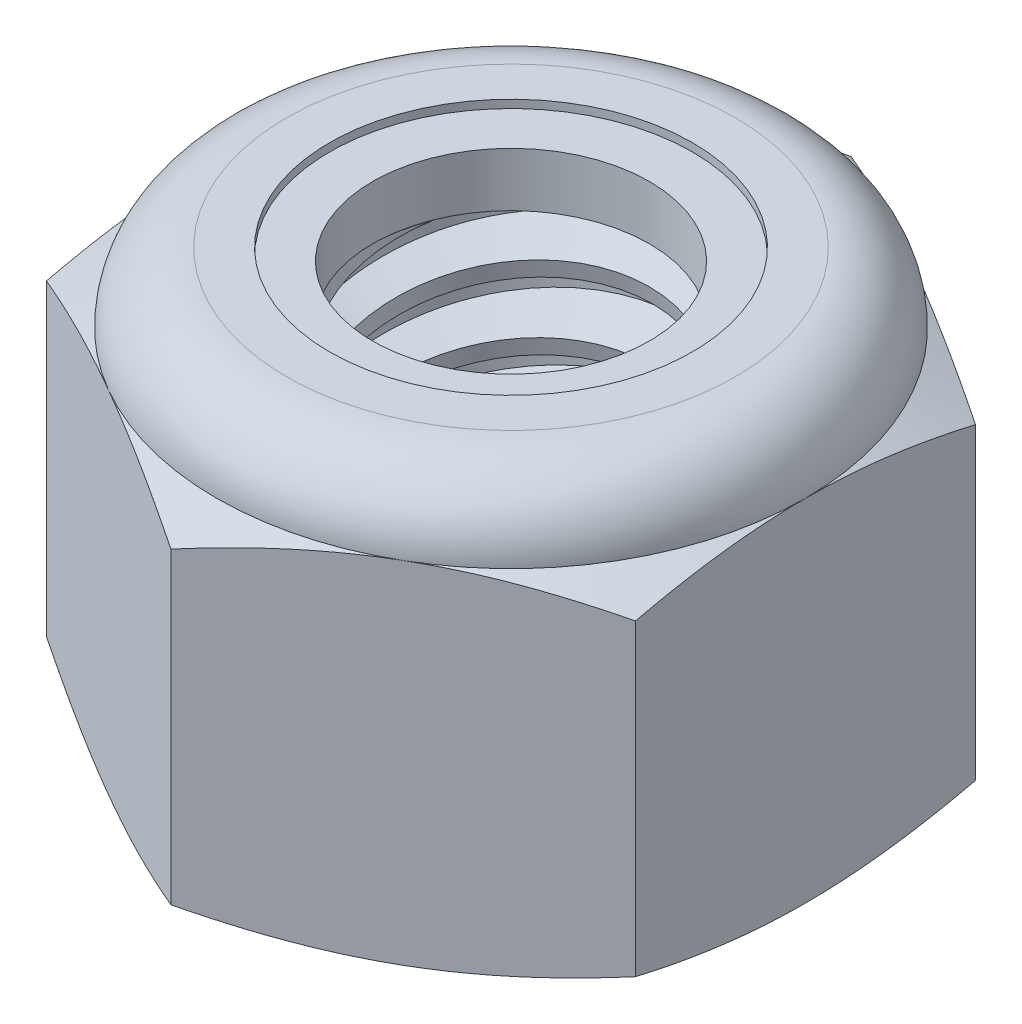
SolidWorks part; units mm, degrees
ref_plane "Front" through (0, 0, 0) normal (0, 0, 1) x (1, 0, 0)
ref_plane "Top" through (0, 0, 0) normal (0, 1, 0) x (1, 0, 0)
ref_plane "Right" through (0, 0, 0) normal (1, 0, 0) x (0, 0, -1)
sketch "Sketch1" plane through (0, 0, 0) normal (0, 1, 0) x (1, 0, 0)
  line L1 (0, 6.4158) -> (-5.5563, 3.2079)
  line L2 (-5.5563, 3.2079) -> (-5.5563, -3.2079)
  line L3 (-5.5563, -3.2079) -> (0, -6.4158)
  line L4 (0, -6.4158) -> (5.5562, -3.2079)
  line L5 (5.5562, -3.2079) -> (5.5562, 3.2079)
  line L6 (5.5562, 3.2079) -> (0, 6.4158)
  circle A0 centre (0, 0) radius 5.5563 construction
  dimension "Hex Flats" = 11.1125
extrude "Extrude1" add sketch "Sketch1" along normal blind 7.9375
sketch "Sketch2" plane through (0, 0, 0) normal (1, 0, 0) x (0, 0, -1)
  line L0 (-3.175, 0) -> (-3.175, 7.9375) construction
  line L1 (0, 0) -> (3.175, 0)
  line L2 (0, 0) -> (0, 7.9375)
  line L3 (0, 7.9375) -> (3.175, 7.9375)
  line L4 (3.175, 0) -> (3.175, 7.9375)
  line L5 (-3.2079, 7.9375) -> (3.2079, 7.9375) construction
  line L7 (0, -3.175) -> (0, 0) construction
  dimension "Thread Dia" = 6.35
revolve "Revolve1" add sketch "Sketch2" angle 360 about L7
sketch "Sketch3" plane through (0, 0, 0) normal (1, 0, 0) x (0, 0, -1)
  line L0 (3.175, 7.9375) -> (-3.175, 7.9375) construction
  line L1 (-3.175, 7.9375) -> (-3.175, 6.6675) construction
  line L2 (-3.175, 6.6675) -> (3.175, 7.9375) construction
  line L3 (3.175, 7.9375) -> (3.2061, 7.7818) construction
  line L4 (3.2061, 7.7818) -> (3.4241, 6.6922)
  line L5 (3.4241, 6.6922) -> (2.6722, 6.9465)
  line L6 (2.6722, 6.9465) -> (2.6099, 7.2579)
  line L7 (2.6099, 7.2579) -> (3.2061, 7.7818)
  line L8 (2.641, 7.1022) -> (3.3151, 7.237) construction
  line L9 (3.175, 7.9375) -> (3.175, 7.209) construction
  line L10 (3.175, 7.209) -> (-3.175, 5.939) construction
  line L11 (-3.175, 5.939) -> (-3.175, 6.6675) construction
  line L12 (-0.2727, 7.9375) -> (0.2727, 5.2105) construction
  line L13 (-3.175, 0) -> (-3.175, 7.9375) construction
  line L14 (0, 7.9375) -> (3.175, 7.9375) construction
  line L15 (3.175, 0) -> (3.175, 7.9375) construction
  point P13 (0, 6.574)
  dimension "D1" = 0.1588
  dimension "D2" = 0.3175
  dimension "Thread Pitch" = 1.27
  dimension "D4" = 60
  dimension "D5" = 1.27
revolve "Cut-Revolve1" cut sketch "Sketch3" angle 360 about L12
pattern_linear "LPattern1" count 6 spacing 1.27 along (0, -1, 0) count 2 spacing 1.27 along (0, 1, 0) of "Cut-Revolve1"
sketch "Sketch4" plane through (0, 0, 0) normal (1, 0, 0) x (0, 0, -1)
  line L0 (0, 7.9375) -> (3.175, 7.9375)
  line L1 (3.175, 7.9375) -> (2.6099, 7.674)
  line L2 (2.6099, 7.674) -> (2.6099, 0.2635)
  line L3 (2.6099, 0.2635) -> (3.175, 0)
  line L4 (3.175, 0) -> (0, 0)
  line L5 (0, 0) -> (0, 7.9375)
  line L6 (3.175, 0) -> (3.175, 7.9375) construction
  line L7 (0, 7.9375) -> (3.175, 7.9375) construction
  line L8 (0, 0) -> (3.175, 0) construction
  line L9 (0, 0) -> (0, 7.9375) construction
  line L10 (0, 7.9375) -> (0, 8.561) construction
  dimension "D1" = 25
revolve "Cut-Revolve2" cut sketch "Sketch4" angle 360 about L10
combine bodies "Combine1" operation type subtract main body 112 bodies to subtract 111
sketch "Sketch5" plane through (0, 0, 0) normal (1, 0, 0) x (0, 0, -1)
  line L0 (0, 0) -> (5.5563, 0)
  line L1 (5.5563, 0) -> (6.4158, 0.4008)
  line L2 (6.4158, 0.4008) -> (6.4158, 6.2138)
  line L3 (6.4158, 6.2138) -> (5.5563, 6.6146)
  line L4 (4.2333, 7.9375) -> (4.2333, 9.2075)
  line L5 (4.2333, 9.2075) -> (7.6858, 9.2075)
  line L6 (7.6858, 9.2075) -> (7.6858, -1.27)
  line L7 (7.6858, -1.27) -> (0, -1.27)
  line L8 (0, -1.27) -> (0, 0)
  line L9 (5.5563, 6.6146) -> (5.5563, 0) construction
  line L10 (0, 0) -> (3.175, 0) construction
  line L13 (6.4158, 3.3073) -> (7.6858, 3.3073) construction
  line L14 (6.4158, 7.9375) -> (6.4158, 0) construction
  line L15 (0, 0) -> (0, 9.2075) construction
  line L20 (0, 9.2075) -> (4.2333, 9.2075) construction
  line L22 (0, 7.9375) -> (3.175, 7.9375) construction
  arc A0 (5.5563, 6.6146) -> (4.2333, 7.9375) centre (4.2333, 6.6146) ccw
  dimension "D1" = 25
  dimension "D2" = 1.27
  dimension "D3" = 7.9375
  dimension "D4" = 1.3229
revolve "Cut-Revolve3" cut sketch "Sketch5" angle 360 about L15
sketch "Sketch6" plane through (0, 0, 0) normal (1, 0, 0) x (0, 0, -1)
  line L0 (0, 6.6146) -> (5.4039, 6.6146)
  line L1 (4.2333, 7.7851) -> (3.4216, 7.7851)
  line L2 (0, 9.2075) -> (0, 6.6146)
  line L3 (3.4216, 9.2075) -> (0, 9.2075)
  line L4 (0, 9.2075) -> (4.2333, 9.2075) construction
  line L5 (0, 0) -> (0, 9.2075) construction
  line L6 (0, 9.2075) -> (0, 44.323) construction
  line L7 (3.4216, 7.7851) -> (3.4216, 9.2075)
  line L8 (4.2333, 7.9375) -> (4.2333, 7.7851) construction
  line L9 (3.4216, 7.7851) -> (2.6099, 7.7851) construction
  line L10 (2.6099, 7.7851) -> (2.6099, 7.674) construction
  arc A0 (5.4039, 6.6146) -> (4.2333, 7.7851) centre (4.2333, 6.6146) ccw
  arc A1 (5.5563, 6.6146) -> (4.2333, 7.9375) centre (4.2333, 6.6146) ccw construction
  dimension "D1" = 0.1524
revolve "Cut-Revolve4" cut sketch "Sketch6" angle 360 about L6
sketch "Sketch7" plane through (0, 0, 0) normal (1, 0, 0) x (0, 0, -1)
  line L0 (2.6099, 6.6908) -> (5.325, 6.6908)
  line L1 (4.2333, 7.7089) -> (2.6099, 7.7089)
  line L2 (2.6099, 7.7089) -> (2.6099, 6.6908)
  line L3 (2.6099, 6.6908) -> (0, 6.6908) construction
  line L4 (0, 6.6908) -> (0, 7.7089) construction
  line L5 (0, 7.7089) -> (2.6099, 7.7089) construction
  line L6 (2.6099, 6.6908) -> (2.6099, 6.6146) construction
  line L7 (0, 6.6146) -> (5.4039, 6.6146) construction
  line L8 (4.2333, 7.7089) -> (4.2333, 7.7851) construction
  arc A0 (5.325, 6.6908) -> (4.2333, 7.7089) centre (4.2333, 6.6146) ccw
  arc A2 (5.4039, 6.6146) -> (4.2333, 7.7851) centre (4.2333, 6.6146) ccw construction
  dimension "D1" = 0.0762
revolve "Revolve2" add sketch "Sketch7" angle 360 about L4
equation "\"D1@Sketch3\"=\"Thread Pitch@Sketch3\"/8"
equation "\"D2@Sketch3\"=\"Thread Pitch@Sketch3\"/4"
equation "\"D5@Sketch3\"=\"Thread Pitch@Sketch3\""
equation "\"D4@LPattern1\"=\"Thread Pitch@Sketch3\""
equation "\"D3@LPattern1\"=\"Thread Pitch@Sketch3\""
equation "\"D1@LPattern1\"=\"Height@Extrude1\"/\"Thread Pitch@Sketch3\""
equation "\"D4@Sketch5\"=\"Height@Extrude1\"/6"
